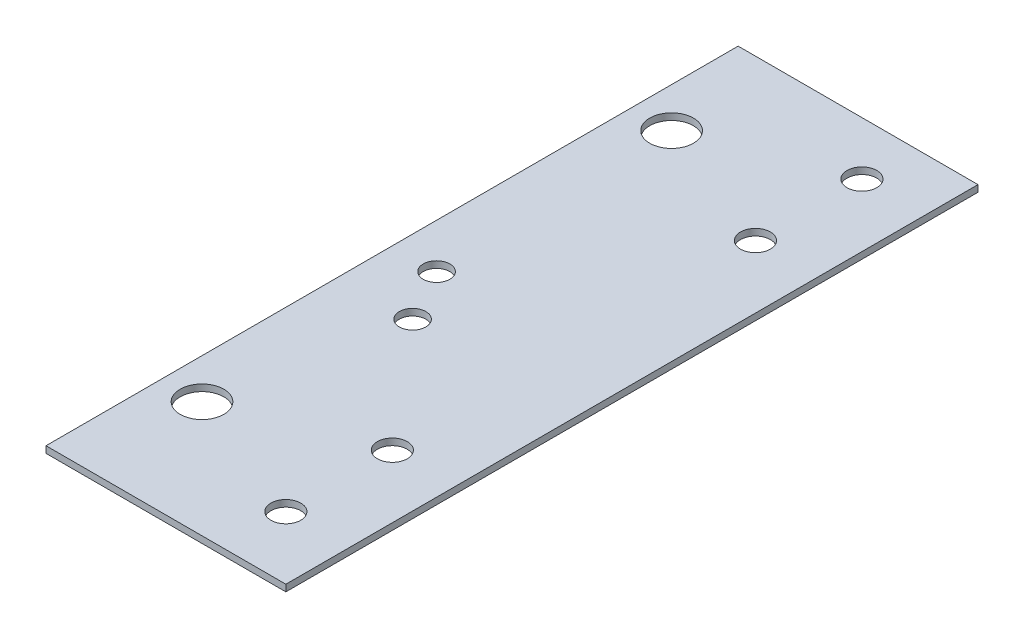
SolidWorks part; units mm, degrees
ref_plane "Front Plane" through (0, 0, 0) normal (0, 0, 1) x (1, 0, 0)
ref_plane "Top Plane" through (0, 0, 0) normal (0, 1, 0) x (1, 0, 0)
ref_plane "Right Plane" through (0, 0, 0) normal (1, 0, 0) x (0, 0, -1)
sketch "Sketch1" plane through (0, 0, 0) normal (0, 1, 0) x (1, 0, 0)
  line L0 (-19.0817, 56.007) -> (-19.0817, -56.007) construction
  line L1 (-28.6068, 81.407) -> (28.6068, 81.407)
  line L2 (-28.6068, 81.407) -> (-28.6068, -81.407)
  line L3 (-28.6068, -81.407) -> (28.6068, -81.407) construction
  line L4 (28.6068, 81.407) -> (28.6068, -81.407)
  line L5 (-28.6068, 81.407) -> (28.6068, -81.407) construction
  line L6 (-28.6068, -81.407) -> (28.6068, 81.407) construction
  line L7 (-19.0817, 0) -> (0, 0) construction
  line L8 (13.6208, -68.707) -> (13.6208, 68.707) construction
  line L9 (-19.0817, -56.007) -> (60.5742, -56.007) construction
  line L10 (-19.0817, 56.007) -> (37.012, 56.007) construction
  line L11 (-28.6068, -81.407) -> (-28.6068, -83.693)
  line L12 (-28.6068, -83.693) -> (28.6068, -83.693)
  line L13 (28.6068, -83.693) -> (28.6068, -81.407)
  circle A0 centre (-19.0817, 56.007) radius 5.207
  circle A1 centre (-19.0817, -56.007) radius 5.207
  circle A2 centre (13.6208, 68.707) radius 3.556
  circle A3 centre (13.6208, 43.307) radius 3.556
  circle A4 centre (13.6208, -43.307) radius 3.556
  circle A5 centre (13.6208, -68.707) radius 3.556
  point P0 (0, 0)
  dimension "D1" = 112.014
  dimension "D2" = 10.414
  dimension "D3" = 7.112
  dimension "D4" = 25.4
  dimension "D5" = 25.4
  dimension "D6" = 12.7
  dimension "D7" = 12.7
  dimension "D8" = 32.7025
  dimension "D9" = 14.986
  dimension "D10" = 9.525
  dimension "D11" = 12.7
  dimension "D12" = 165.1
extrude "Boss-Extrude1" add sketch "Sketch1" along normal blind 1.5875
sketch "Sketch2" plane through (0, 1.5875, 0) normal (0, 1, 0) x (1, 0, 0)
  line L0 (-28.6068, -1.143) -> (28.6067, -1.143) construction
  line L1 (-28.6068, 81.407) -> (-28.6068, -83.693) construction
  line L2 (28.6068, -83.693) -> (28.6068, 81.407) construction
  circle A1 centre (-17.9928, -1.143) radius 3.175
  dimension "D2" = 10.6139
  dimension "D3" = 6.35
extrude "Cut-Extrude1" cut sketch "Sketch2" against normal through all
sketch "Sketch3" plane through (0, 0, 0) normal (0, -1, 0) x (1, 0, 0)
  line L0 (-28.6068, -81.407) -> (-28.6068, 83.693) construction
  line L1 (28.6067, 1.143) -> (-28.6068, 1.143) construction
  line L2 (28.6068, 83.693) -> (28.6068, -81.407) construction
  circle A0 centre (-11.0173, 13.843) radius 3.175
  dimension "D1" = 17.5895
  dimension "D2" = 6.35
  dimension "D3" = 12.7
extrude "Cut-Extrude2" cut sketch "Sketch3" against normal through all
